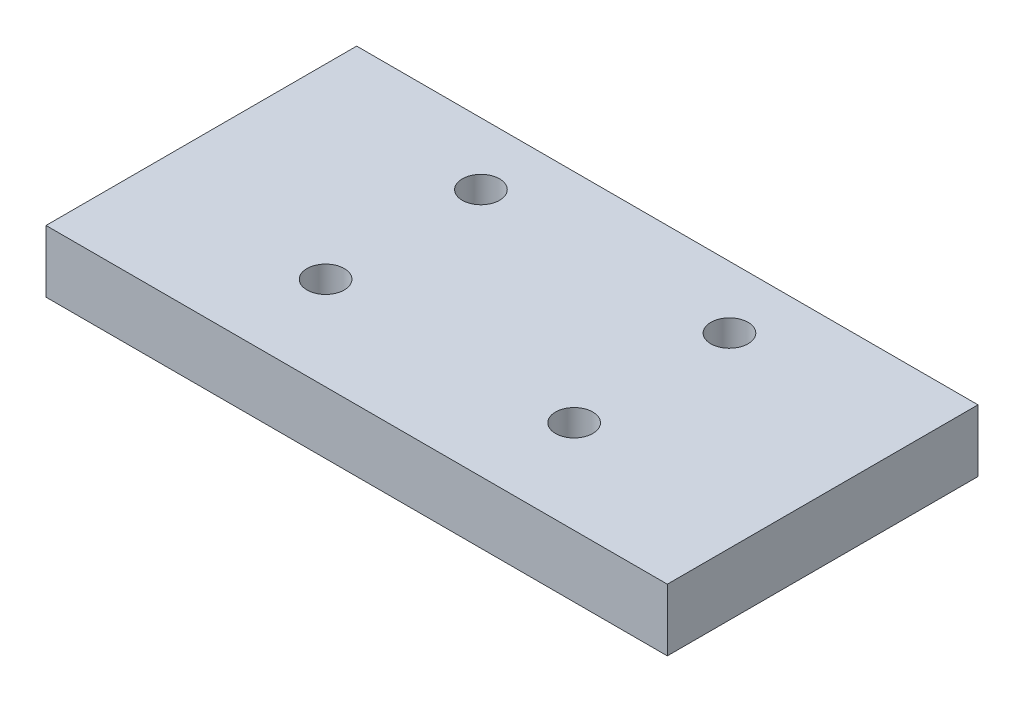
SolidWorks part; units mm, degrees
ref_plane "Front Plane" through (0, 0, 0) normal (0, 0, 1) x (1, 0, 0)
ref_plane "Top Plane" through (0, 0, 0) normal (0, 1, 0) x (1, 0, 0)
ref_plane "Right Plane" through (0, 0, 0) normal (1, 0, 0) x (0, 0, -1)
sketch "Sketch1" plane through (0, 0, 0) normal (0, 1, 0) x (1, 0, 0)
  line L36 (0, 0) -> (100, 0)
  line L41 (100, 0) -> (100, 50)
  line L42 (100, 50) -> (0, 50)
  line L43 (0, 50) -> (0, 0)
  circle A0 centre (70, 15) radius 3
  circle A1 centre (30, 15) radius 3
  circle A6 centre (30, 40) radius 3
  circle A7 centre (70, 40) radius 3
  point P6 (0, 0)
  point P7 (0, 0)
  point P8 (0, 0)
  point P9 (0, 0)
  point P10 (0, 0)
  point P12 (0, 0)
  point P14 (0, 0)
  point P15 (0, 0)
  dimension "D1" = 10
  dimension "D2" = 15
extrude "Boss-Extrude1" add sketch "Sketch1" along normal blind 10
